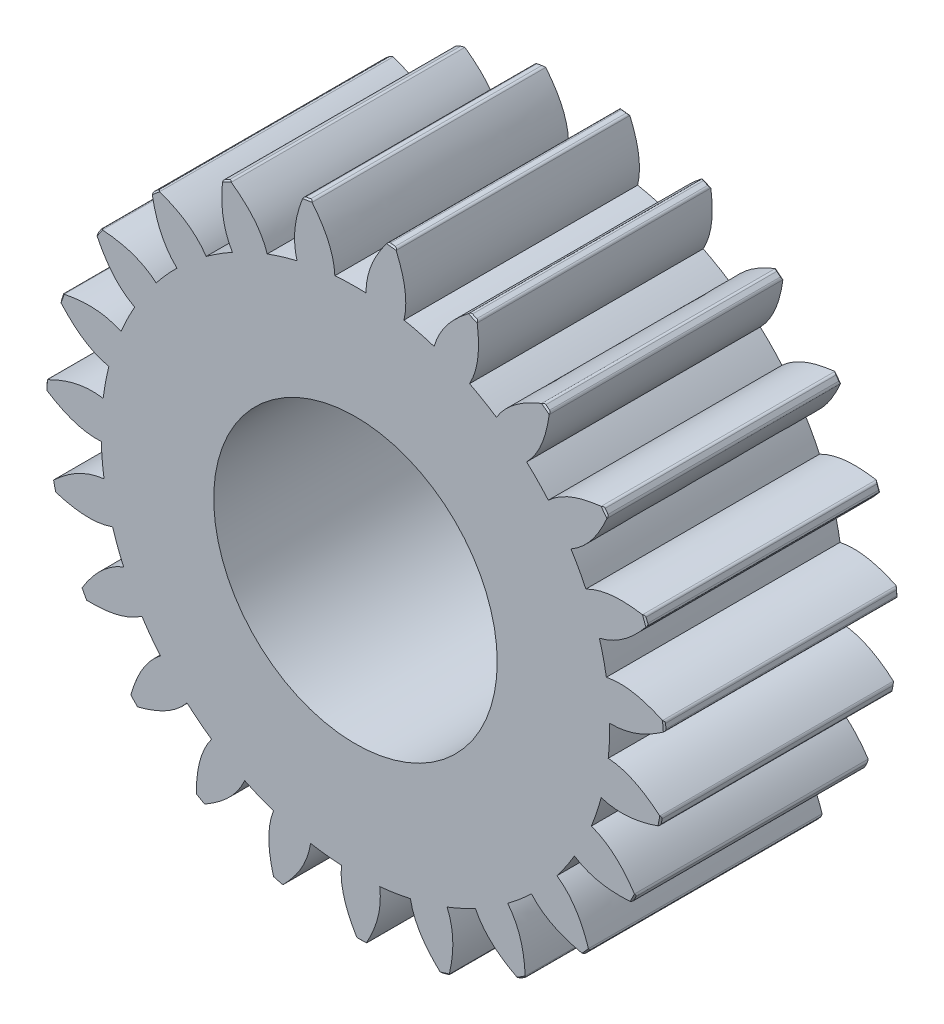
SolidWorks part; units mm, degrees
ref_plane "Front Plane" through (0, 0, 0) normal (0, 0, 1) x (1, 0, 0)
ref_plane "Top Plane" through (0, 0, 0) normal (0, 1, 0) x (1, 0, 0)
ref_plane "Right Plane" through (0, 0, 0) normal (1, 0, 0) x (0, 0, -1)
sketch "Sketch1" plane through (0, 0, 0) normal (0, 0, 1) x (1, 0, 0)
  line L0 (-8.5607, 36.6382) -> (-5.8227, 36.8658) construction
  line L1 (2.3915, 37.5489) -> (13.1396, 35.2561) construction
  line L2 (13.1396, 35.2561) -> (22.7667, 29.9552) construction
  line L3 (22.7667, 29.9552) -> (30.4514, 22.0987) construction
  line L4 (2.3915, 37.5489) -> (-8.5763, 38.2475) construction
  line L5 (13.1396, 35.2561) -> (-7.4565, 42.9321) construction
  line L6 (22.7667, 29.9552) -> (-3.4824, 49.9053) construction
  line L7 (30.4514, 22.0987) -> (4.632, 57.6773) construction
  line L8 (0, 0) -> (-2.973, 35.7516) construction
  line L10 (0, 0) -> (-5.8227, 36.8658) construction
  circle A0 centre (0, 0) radius 35.875
  circle A1 centre (0, 0) radius 40.25 construction
  circle A2 centre (0, 0) radius 37.625
  arc A3 (-6.2674, 43.2988) -> (-7.3822, 43.1227) centre (0, 0) ccw
  spline S0 degree 3 poles (-8.2496, 34.9136) (-8.4096, 35.4882) (-8.6048, 36.6026) (-8.6192, 39.3202) (-8.0187, 41.4896) (-7.4072, 43.0593) (-7.3822, 43.1227) knots -0.066908 -0.066908 -0.066908 -0.066908 0 0.062651 0.250154 0.258064 0.258064 0.258064 0.258064
  spline S1 degree 3 poles (-2.9122, 35.7566) (-2.9371, 36.3525) (-3.0948, 37.4729) (-3.9187, 40.0626) (-5.1586, 41.9413) (-6.224, 43.2461) (-6.2674, 43.2988) knots -0.066908 -0.066908 -0.066908 -0.066908 0 0.062651 0.250154 0.258064 0.258064 0.258064 0.258064
  spline S2 degree 2 poles (-3.4824, 49.9053) (-0.0417, 54.3807) (4.632, 57.6773) knots 0.562599 0.562599 0.562599 1 1 1
  dimension "D1" = 87.5
  dimension "D2" = 80.5
  dimension "D3" = 75.25
  dimension "D4" = 71.75
  dimension "D5" = 10.99
  dimension "D6" = 10.99
  dimension "D7" = 21.98
  dimension "D8" = 32.97
  dimension "D9" = 43.96
extrude "Boss-Extrude2" add sketch "Sketch1" along normal blind 32.97 contours A2 S1 A3 S0 | A0 S1 A2 S0 | A0 A3
chamfer "Chamfer1" distance 0.2 angle 45 2 edges at (-6.8254, 43.2143, 0) (-6.8254, 43.2143, 32.97)
fillet "Fillet1" radius 0.4 2 edges at (-7.3822, 43.1227, 16.485) (-6.2674, 43.2988, 16.485)
pattern_circular "CirPattern1" count 23 over 360 of "Boss-Extrude2", "Chamfer1", "Fillet1"
sketch "Sketch2" plane through (0, 0, 32.97) normal (0, 0, 1) x (1, 0, 0)
  circle A0 centre (0, 0) radius 20
  dimension "D1" = 40
extrude "Cut-Extrude1" cut sketch "Sketch2" against normal through all
